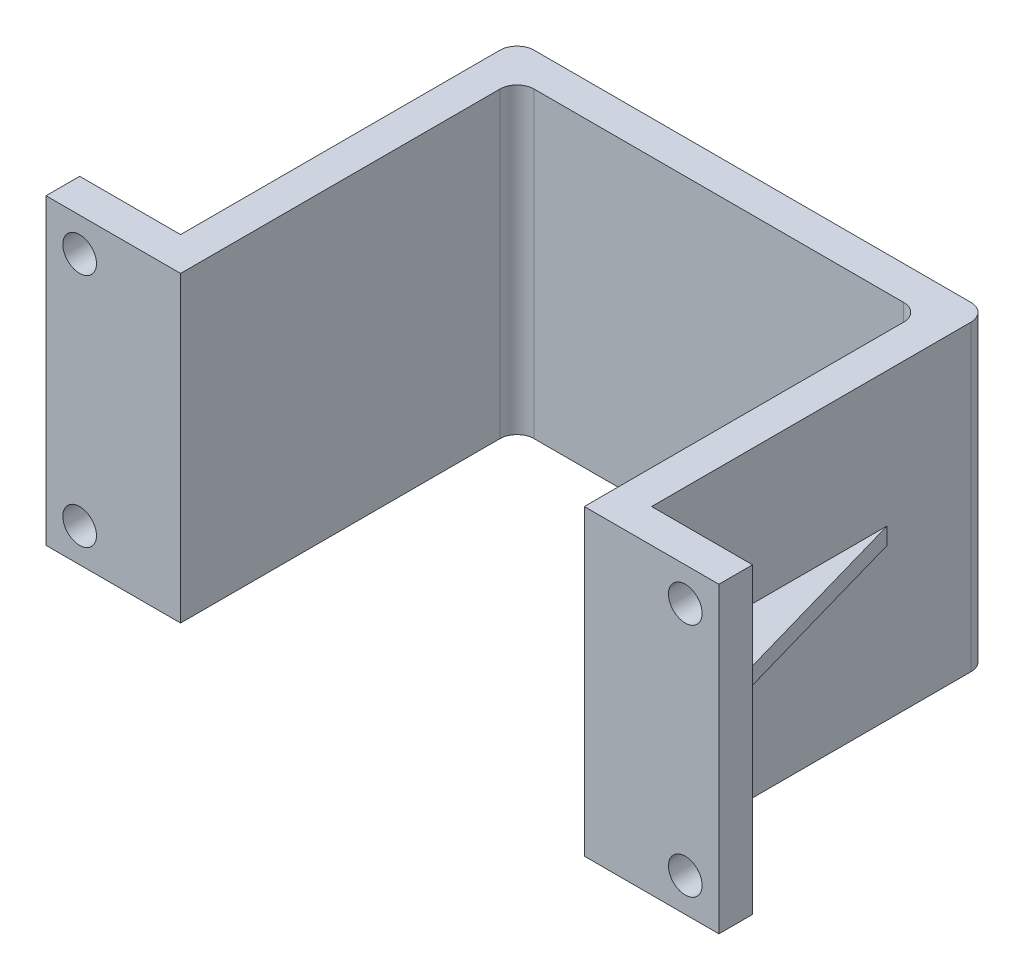
SolidWorks part; units mm, degrees
ref_plane "Front Plane" through (0, 0, 0) normal (0, 0, 1) x (1, 0, 0)
ref_plane "Top Plane" through (0, 0, 0) normal (0, 1, 0) x (1, 0, 0)
ref_plane "Right Plane" through (0, 0, 0) normal (1, 0, 0) x (0, 0, -1)
sketch "Sketch1" plane through (0, 0, 0) normal (0, 1, 0) x (1, 0, 0)
  line L0 (12.508, 0) -> (14.2915, 0)
  line L2 (0, 0.508) -> (0, 9.492)
  line L3 (0.508, 10) -> (11.492, 10)
  line L4 (12, 0.508) -> (12, 9.492)
  line L5 (-0.9045, 0) -> (-0.508, 0)
  line L6 (-1, 1.508) -> (-1, 10.492)
  line L7 (-0.492, 11) -> (12.492, 11)
  line L8 (13, 1.508) -> (13, 10.492)
  line L9 (-0.508, 0) -> (0, 0)
  line L10 (-0.9045, 0) -> (-4, 0)
  line L12 (-1.508, 1) -> (-4, 1)
  line L13 (-4, 0) -> (-4, 1)
  line L14 (14.2915, 0) -> (16, 0)
  line L16 (13.508, 1) -> (16, 1)
  line L17 (16, 0) -> (16, 1)
  line L18 (0, 0) -> (0, 0.508)
  line L19 (13, 1.508) -> (13, 1)
  line L20 (13, 1) -> (13.508, 1)
  line L21 (12, 0.508) -> (12, 0)
  line L22 (12, 0) -> (12.508, 0)
  line L23 (-1, 1.508) -> (-1, 1)
  line L24 (-1, 1) -> (-1.508, 1)
  arc A4 (11.492, 10) -> (12, 9.492) centre (11.492, 9.492) cw
  arc A5 (0, 9.492) -> (0.508, 10) centre (0.508, 9.492) cw
  arc A6 (12.492, 11) -> (13, 10.492) centre (12.492, 10.492) cw
  arc A7 (-1, 10.492) -> (-0.492, 11) centre (-0.492, 10.492) cw
  point P17 (0, 0)
  point P20 (12, 0)
  point P23 (13, 1)
  point P26 (-1, 1)
  point P29 (12, 10)
  point P32 (0, 10)
  dimension "D1" = 12
  dimension "D2" = 10
  dimension "D3" = 1
  dimension "D4" = 1
  dimension "D5" = 1
  dimension "D6" = 3
  dimension "D7" = 3
  dimension "D8" = 1
  dimension "D9" = 1
extrude "Boss-Extrude1" add sketch "Sketch1" along normal blind 9
sketch "Sketch2" plane through (0, 0, -1) normal (0, 0, -1) x (-1, 0, 0)
  line L0 (1, 0) -> (4, 0) construction
  line L1 (4, 9) -> (4, 0) construction
  line L2 (1, 9) -> (4, 9) construction
  line L3 (-16, 0) -> (-13, 0) construction
  line L4 (-16, 9) -> (-16, 0) construction
  line L5 (-16, 9) -> (-13, 9) construction
  circle A0 centre (3, 1) radius 0.5
  circle A1 centre (3, 8) radius 0.5
  circle A2 centre (-15, 1) radius 0.5
  circle A3 centre (-15, 8) radius 0.5
  dimension "D9" = 1
  dimension "D10" = 1
  dimension "D11" = 1
  dimension "D12" = 1
  dimension "D1" = 1
  dimension "D2" = 1
  dimension "D3" = 1
  dimension "D4" = 1
  dimension "D5" = 1
  dimension "D6" = 1
  dimension "D7" = 1
  dimension "D8" = 1
extrude "Cut-Extrude1" cut sketch "Sketch2" against normal blind 9
ref_plane "Plane1" through (0, 4.5, 0) normal (0, 1, 0) x (1, 0, 0)
sketch "Sketch3" plane through (0, 4.5, 0) normal (0, 1, 0) x (1, 0, 0)
  line L0 (-3, 1) -> (-1, 8)
  line L1 (-1, 1) -> (-4, 1) construction
  line L2 (-1, 10.492) -> (-1, 1) construction
  line L3 (-1, 8) -> (-1, 1)
  line L4 (-1, 1) -> (-3, 1)
  line L5 (13, 8) -> (13, 1)
  line L6 (13, 1) -> (13, 10.492) construction
  line L7 (13, 1) -> (15, 1)
  line L8 (16, 1) -> (13, 1) construction
  line L9 (15, 1) -> (13, 8)
  point P13 (12.899, 8)
  dimension "D1" = 2
  dimension "D2" = 7
  dimension "D3" = 7
  dimension "D4" = 2
extrude "Boss-Extrude2" add sketch "Sketch3" along normal blind 0.5
